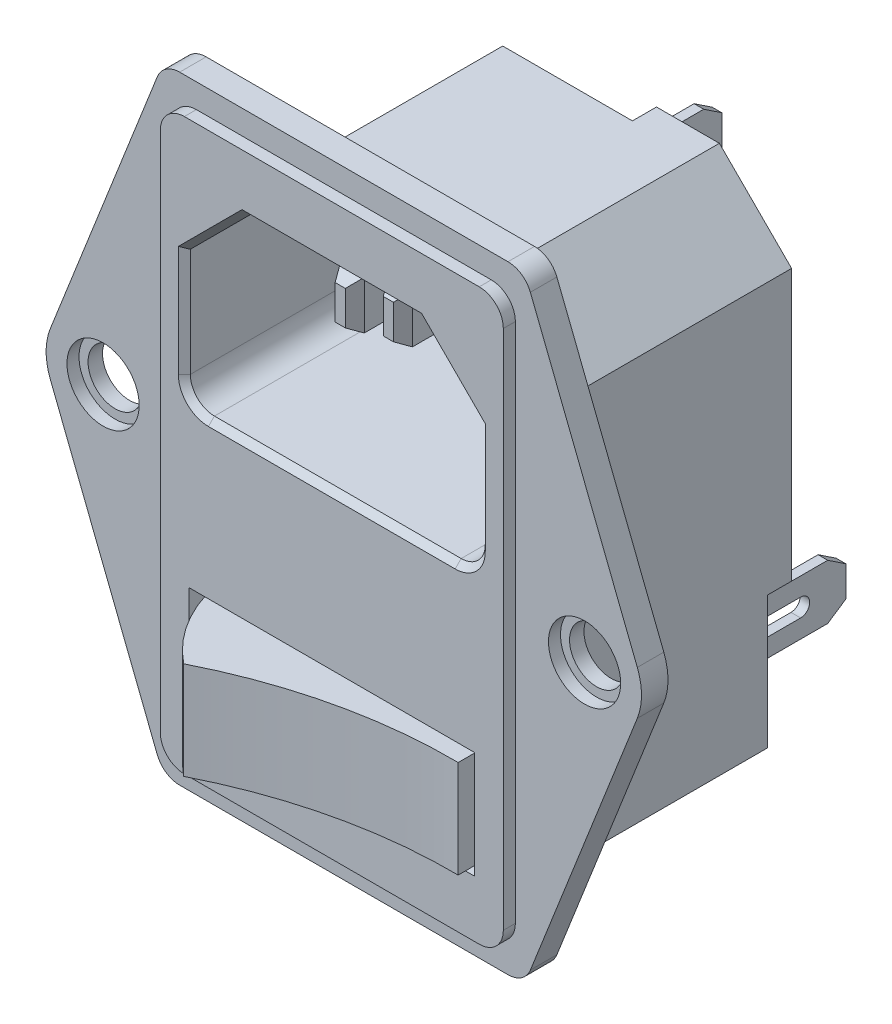
SolidWorks part; units mm, degrees
ref_plane "Спереди" through (0, 0, 0) normal (0, 0, 1) x (1, 0, 0)
ref_plane "Сверху" through (0, 0, 0) normal (0, 1, 0) x (1, 0, 0)
ref_plane "Справа" through (0, 0, 0) normal (1, 0, 0) x (0, 0, -1)
sketch "Эскиз1" plane through (0, 0, 0) normal (0, 0, 1) x (1, 0, 0)
  line L0 (-15, 25.65) -> (-25.1038, 0)
  line L1 (-15, -25.65) -> (15, -25.65)
  line L2 (-15, -25.65) -> (-15, 25.65) construction
  line L3 (-15, 25.65) -> (15, 25.65)
  line L4 (15, -25.65) -> (15, 25.65) construction
  line L5 (-15, -25.65) -> (15, 25.65) construction
  line L6 (-15, 25.65) -> (15, -25.65) construction
  line L7 (-25.1038, 0) -> (-15, -25.65)
  line L8 (0, 0) -> (0, 25.65) construction
  line L9 (25.1038, 0) -> (15, -25.65)
  line L10 (15, 25.65) -> (25.1038, 0)
  point P0 (0, 0)
  dimension "D1" = 51.3
  dimension "D2" = 30
  dimension "D3" = 137
  dimension "D4" = 68.5
extrude "Бобышка-Вытянуть1" add sketch "Эскиз1" along normal blind 2.2
sketch "Эскиз2" plane through (0, 0, 2.2) normal (0, 0, 1) x (1, 0, 0)
  line L1 (-14.25, -23.65) -> (14.25, -23.65)
  line L2 (-14.25, -23.65) -> (-14.25, 23.65)
  line L3 (-14.25, 23.65) -> (14.25, 23.65)
  line L4 (14.25, -23.65) -> (14.25, 23.65)
  line L5 (-14.25, -23.65) -> (14.25, 23.65) construction
  line L6 (-14.25, 23.65) -> (14.25, -23.65) construction
  point P0 (0, 0)
  dimension "D1" = 28.5
  dimension "D2" = 47.3
extrude "Бобышка-Вытянуть2" add sketch "Эскиз2" along normal blind 3.2 from surface at -2.2 starting at face at (0, 0, 0)
sketch "Эскиз3" plane through (0, 0, 2.2) normal (0, 0, 1) x (1, 0, 0)
  line L0 (20, 0) -> (-20, 0) construction
  circle A0 centre (-20, 0) radius 2.25
  circle A1 centre (20, 0) radius 2.25
  point P4 (0, 0)
  point P9 (-22.25, 0)
  point P10 (22.25, 0)
  dimension "D1" = 4.5
  dimension "D2" = 44.5
  dimension "D3" = 40
extrude "Вырез-Вытянуть1" cut sketch "Эскиз3" against normal blind 3.2
sketch "Эскиз4" plane through (0, 0, 2.2) normal (0, 0, 1) x (1, 0, 0)
  circle A0 centre (-20, 0) radius 3
  circle A1 centre (20, 0) radius 3
  dimension "D1" = 6
extrude "Вырез-Вытянуть2" cut sketch "Эскиз4" against normal blind 1
fillet "Скругление1" radius 2 8 edges at (15, 25.65, 1.1) (-15, 25.65, 1.1) (-15, -25.65, 1.1) (15, -25.65, 1.1) (-14.25, 23.65, 2.7) (-14.25, -23.65, 2.7) (14.25, -23.65, 2.7) (14.25, 23.65, 2.7)
fillet "Скругление2" radius 5 2 edges at (25.1038, 0, 1.1) (-25.1038, 0, 1.1)
sketch "Эскиз7" plane through (0, 0, 0) normal (0, 0, -1) x (-1, 0, 0)
  line L0 (-14, 13.75) -> (-8, 19.75)
  line L1 (-14, -19.75) -> (14, -19.75)
  line L2 (-14, -19.75) -> (-14, 13.75)
  line L3 (-8, 19.75) -> (8, 19.75)
  line L4 (14, -19.75) -> (14, 13.75)
  line L5 (-14, -19.75) -> (14, 19.75) construction
  line L6 (-14, 19.75) -> (14, -19.75) construction
  line L7 (8, 19.75) -> (14, 13.75)
  point P0 (0, 0)
  dimension "D1" = 39.5
  dimension "D2" = 28
extrude "Бобышка-Вытянуть3" add sketch "Эскиз7" along normal blind 21
sketch "Эскиз6" plane through (0, 0, 3.2) normal (0, 0, 1) x (1, 0, 0)
  line L0 (-13.6382, -25.65) -> (13.6382, -25.65) construction
  line L1 (-11.85, -18.95) -> (11.85, -18.95)
  line L2 (-11.85, -18.95) -> (-11.85, -10.05)
  line L3 (-11.85, -10.05) -> (11.85, -10.05)
  line L4 (11.85, -18.95) -> (11.85, -10.05)
  line L5 (-11.85, -18.95) -> (11.85, -10.05) construction
  line L6 (-11.85, -10.05) -> (11.85, -18.95) construction
  point P0 (0, -14.5)
  dimension "D1" = 8.9
  dimension "D2" = 23.7
  dimension "D3" = 6.7
extrude "Вырез-Вытянуть3" cut sketch "Эскиз6" against normal blind 3
sketch "Эскиз8" plane through (0, 0, -21) normal (0, 0, -1) x (-1, 0, 0)
  line L0 (8, 19.75) -> (-8, 19.75) construction
  line L1 (-14, -19.75) -> (-8.6, -19.75)
  line L2 (-14, -19.75) -> (-14, -8.75)
  line L3 (-14, -8.75) -> (-8.6, -8.75)
  line L4 (-8.6, -19.75) -> (-8.6, -8.75)
  line L5 (-2.775, 8.35) -> (2.775, 8.35)
  line L6 (-2.775, 8.35) -> (-2.775, 19.75)
  line L7 (-2.775, 19.75) -> (2.775, 19.75)
  line L8 (2.775, 8.35) -> (2.775, 19.75) construction
  line L9 (-2.775, 8.35) -> (2.775, 19.75) construction
  line L10 (-2.775, 19.75) -> (2.775, 8.35) construction
  line L11 (0, 0) -> (0, -19.75) construction
  line L12 (-14, -19.75) -> (14, -19.75) construction
  line L13 (14, -8.75) -> (8.6, -8.75)
  line L14 (8.6, -19.75) -> (8.6, -8.75)
  line L15 (14, -19.75) -> (8.6, -19.75)
  line L16 (14, -19.75) -> (14, -8.75)
  line L17 (2.775, 12.55) -> (14, 12.55)
  line L18 (14, -19.75) -> (14, 13.75) construction
  line L19 (14, 12.55) -> (14, 19.75)
  line L20 (14, 19.75) -> (2.775, 19.75)
  line L21 (2.775, 12.55) -> (2.775, 8.35)
  point P5 (0, 14.05)
  dimension "D1" = 11
  dimension "D2" = 5.4
  dimension "D3" = 7.2
  dimension "D4" = 11.4
  dimension "D5" = 5.55
extrude "Вырез-Вытянуть4" cut sketch "Эскиз8" against normal blind 2
sketch "Эскиз9" plane through (0, 0, -21) normal (0, 0, -1) x (-1, 0, 0)
  line L0 (-14, -19.75) -> (14, -19.75) construction
  line L1 (-1.5, -9.25) -> (1.5, -9.25)
  line L2 (-1.5, -9.25) -> (-1.5, -19.75)
  line L3 (-1.5, -19.75) -> (1.5, -19.75)
  line L4 (1.5, -9.25) -> (1.5, -19.75)
  line L5 (-1.5, -9.25) -> (1.5, -19.75) construction
  line L6 (-1.5, -19.75) -> (1.5, -9.25) construction
  line L7 (-14, 13.75) -> (-14, -8.75) construction
  line L8 (-6.5, 0.25) -> (-3.5, 0.25)
  line L9 (-6.5, 0.25) -> (-6.5, -7.75)
  line L10 (-6.5, -7.75) -> (-3.5, -7.75)
  line L11 (-3.5, 0.25) -> (-3.5, -7.75)
  line L12 (-6.5, 0.25) -> (-3.5, -7.75) construction
  line L13 (-6.5, -7.75) -> (-3.5, 0.25) construction
  line L14 (-9.8, 11.55) -> (-4.3, 11.55)
  line L15 (-9.8, 11.55) -> (-9.8, 6.05)
  line L16 (-9.8, 6.05) -> (-4.3, 6.05)
  line L17 (-4.3, 11.55) -> (-4.3, 6.05)
  line L18 (-9.8, 11.55) -> (-4.3, 6.05) construction
  line L19 (-9.8, 6.05) -> (-4.3, 11.55) construction
  line L20 (8, 19.75) -> (-2.775, 19.75) construction
  line L21 (0, 0) -> (0, 25.65) construction
  line L22 (-13.6382, 25.65) -> (13.6382, 25.65) construction
  line L23 (9.8, 6.05) -> (4.3, 6.05)
  line L24 (4.3, 11.55) -> (4.3, 6.05)
  line L25 (9.8, 11.55) -> (4.3, 11.55)
  line L26 (9.8, 11.55) -> (9.8, 6.05)
  line L27 (6.5, -7.75) -> (3.5, -7.75)
  line L28 (3.5, 0.25) -> (3.5, -7.75)
  line L29 (6.5, 0.25) -> (3.5, 0.25)
  line L30 (6.5, 0.25) -> (6.5, -7.75)
  point P0 (0, -14.5)
  point P7 (-5, -3.75)
  point P12 (-7.05, 8.8)
  dimension "D1" = 5.5
  dimension "D2" = 3
  dimension "D3" = 8
  dimension "D4" = 10.5
  dimension "D5" = 3
  dimension "D6" = 12
  dimension "D7" = 7.5
  dimension "D8" = 4.2
  dimension "D9" = 8.2
extrude "Бобышка-Вытянуть4" add sketch "Эскиз9" along normal blind 2.1
sketch "Эскиз10" plane through (0, 0, -19) normal (0, 0, -1) x (-1, 0, 0)
  line L0 (14, -19.75) -> (14, 13.75) construction
  line L1 (-0.4, 10.7) -> (0.4, 10.7)
  line L2 (-0.4, 10.7) -> (-0.4, 15.25)
  line L3 (-0.4, 15.25) -> (0.4, 15.25)
  line L4 (0.4, 10.7) -> (0.4, 15.25)
  line L5 (-0.4, 10.7) -> (0.4, 15.25) construction
  line L6 (-0.4, 15.25) -> (0.4, 10.7) construction
  line L7 (-10.7, -16.6) -> (-9.9, -16.6)
  line L8 (-10.7, -16.6) -> (-10.7, -12.05)
  line L9 (-10.7, -12.05) -> (-9.9, -12.05)
  line L10 (-9.9, -16.6) -> (-9.9, -12.05)
  line L11 (-10.7, -16.6) -> (-9.9, -12.05) construction
  line L12 (-10.7, -12.05) -> (-9.9, -16.6) construction
  line L13 (9.9, -16.6) -> (10.7, -16.6)
  line L14 (9.9, -16.6) -> (9.9, -12.05)
  line L15 (9.9, -12.05) -> (10.7, -12.05)
  line L16 (10.7, -16.6) -> (10.7, -12.05)
  line L17 (9.9, -16.6) -> (10.7, -12.05) construction
  line L18 (9.9, -12.05) -> (10.7, -16.6) construction
  line L19 (8.6, -19.75) -> (14, -19.75) construction
  line L20 (0, 0) -> (0, -19.75) construction
  line L21 (-14, -19.75) -> (14, -19.75) construction
  line L22 (8, 19.75) -> (-2.775, 19.75) construction
  point P0 (0, 12.975)
  point P5 (10.3, -14.325)
  point P7 (-10.3, -14.325)
  dimension "D1" = 0.8
  dimension "D2" = 4.55
  dimension "D3" = 3.3
  dimension "D4" = 3.15
  dimension "D5" = 4.5
extrude "Бобышка-Вытянуть5" add sketch "Эскиз10" along normal blind 9.8
sketch "Эскиз11" plane through (-10.7, 0, 0) normal (-1, 0, 0) x (0, 0, 1)
  line L0 (-25.05, -14.325) -> (-21.55, -14.325) construction
  line L1 (-25.05, -13.575) -> (-21.55, -13.575)
  line L2 (-25.05, -15.075) -> (-21.55, -15.075)
  line L3 (-28.8, -16.6) -> (-28.8, -12.05) construction
  arc A0 (-25.05, -13.575) -> (-25.05, -15.075) centre (-25.05, -14.325) ccw
  arc A1 (-21.55, -15.075) -> (-21.55, -13.575) centre (-21.55, -14.325) ccw
  point P2 (-23.3, -14.325)
  point P10 (-28.8, -14.325)
  point P11 (-25.8, -14.325)
  dimension "D1" = 1.5
  dimension "D2" = 3.5
  dimension "D3" = 3
extrude "Вырез-Вытянуть5" cut sketch "Эскиз11" against normal up to surface (0.8 mm away) up to face at (-9.9, -14.325, -23.9)
sketch "Эскиз12" plane through (10.7, 0, 0) normal (1, 0, 0) x (0, 0, -1)
  line L2 (25.05, -13.575) -> (21.55, -13.575)
  line L3 (21.55, -15.075) -> (25.05, -15.075)
  line L4 (25.05, -13.575) -> (21.55, -13.575)
  line L5 (21.55, -15.075) -> (25.05, -15.075)
  arc A2 (21.55, -13.575) -> (21.55, -15.075) centre (21.55, -14.325) ccw
  arc A3 (25.05, -15.075) -> (25.05, -13.575) centre (25.05, -14.325) ccw
  arc A4 (21.55, -13.575) -> (21.55, -15.075) centre (21.55, -14.325) ccw
  arc A5 (25.05, -15.075) -> (25.05, -13.575) centre (25.05, -14.325) ccw
  dimension "D1" = 0
extrude "Вырез-Вытянуть6" cut sketch "Эскиз12" against normal up to surface (0.8 mm away) up to face at (9.9, -14.325, -23.9)
sketch "Эскиз13" plane through (-0.4, 0, 0) normal (-1, 0, 0) x (0, 0, 1)
  line L0 (-21.55, 12.975) -> (-25.05, 12.975) construction
  line L1 (-21.55, 12.225) -> (-25.05, 12.225)
  line L2 (-21.55, 13.725) -> (-25.05, 13.725)
  line L3 (-28.8, 10.7) -> (-28.8, 15.25) construction
  arc A0 (-21.55, 12.225) -> (-21.55, 13.725) centre (-21.55, 12.975) ccw
  arc A1 (-25.05, 13.725) -> (-25.05, 12.225) centre (-25.05, 12.975) ccw
  point P2 (-23.3, 12.975)
  point P10 (-28.8, 12.975)
  point P12 (-25.8, 12.975)
  dimension "D1" = 1.5
  dimension "D2" = 3.5
  dimension "D3" = 3
extrude "Вырез-Вытянуть7" cut sketch "Эскиз13" against normal up to surface (0.8 mm away) up to face at (0.4, 12.975, -23.9)
chamfer "Фаска1" distance 1.5 distance2 1 6 edges at (0, 15.25, -28.8) (0, 10.7, -28.8) (-10.3, -16.6, -28.8) (-10.3, -12.05, -28.8) (10.3, -12.05, -28.8) (10.3, -16.6, -28.8)
sketch "Эскиз14" plane through (0, 0, 3.2) normal (0, 0, 1) x (1, 0, 0)
  line L0 (13.6382, 25.65) -> (-13.6382, 25.65) construction
  line L1 (-10.25, 2.85) -> (10.25, 2.85)
  line L2 (-12.25, 4.85) -> (-12.25, 13.85)
  line L3 (-7.25, 18.85) -> (7.25, 18.85)
  line L4 (12.25, 4.85) -> (12.25, 13.85)
  line L5 (-12.25, 2.85) -> (12.25, 18.85) construction
  line L6 (-12.25, 18.85) -> (12.25, 2.85) construction
  line L7 (-12.25, 13.85) -> (-7.25, 18.85)
  line L8 (7.25, 18.85) -> (12.25, 13.85)
  arc A0 (10.25, 2.85) -> (12.25, 4.85) centre (10.25, 4.85) ccw
  arc A1 (-10.25, 2.85) -> (-12.25, 4.85) centre (-10.25, 4.85) cw
  point P0 (0, 10.85)
  dimension "D4" = 2
  dimension "D1" = 24.5
  dimension "D2" = 16
  dimension "D3" = 6.8
extrude "Вырез-Вытянуть8" cut sketch "Эскиз14" against normal blind 19.7
chamfer "Фаска2" distance 0.5 angle 45 8 edges at (12.25, 9.35, 3.2) (11.6642, 3.4358, 3.2) (0, 2.85, 3.2) (-11.6642, 3.4358, 3.2) (9.75, 16.35, 3.2) (0, 18.85, 3.2) (-9.75, 16.35, 3.2) (-12.25, 9.35, 3.2)
sketch "Эскиз15" plane through (0, 0, -16.5) normal (0, 0, 1) x (1, 0, 0)
  line L0 (0, 12.85) -> (0, 0) construction
  line L1 (-1, 14.85) -> (1, 14.85)
  line L2 (-1, 14.85) -> (-1, 10.85)
  line L3 (-1, 10.85) -> (1, 10.85)
  line L4 (1, 14.85) -> (1, 10.85)
  line L5 (-1, 14.85) -> (1, 10.85) construction
  line L6 (-1, 10.85) -> (1, 14.85) construction
  line L7 (-8, 6.85) -> (-6, 6.85)
  line L8 (-8, 6.85) -> (-8, 10.85)
  line L9 (-8, 10.85) -> (-6, 10.85)
  line L10 (-6, 6.85) -> (-6, 10.85)
  line L11 (-8, 6.85) -> (-6, 10.85) construction
  line L12 (-8, 10.85) -> (-6, 6.85) construction
  line L13 (6, 6.85) -> (8, 6.85)
  line L14 (6, 6.85) -> (6, 10.85)
  line L15 (6, 10.85) -> (8, 10.85)
  line L16 (8, 6.85) -> (8, 10.85)
  line L17 (6, 6.85) -> (8, 10.85) construction
  line L18 (6, 10.85) -> (8, 6.85) construction
  line L19 (-10.25, 2.85) -> (10.25, 2.85) construction
  point P0 (0, 12.85)
  point P5 (-7, 8.85)
  point P10 (7, 8.85)
  dimension "D1" = 2
  dimension "D2" = 4
  dimension "D3" = 4
  dimension "D4" = 8
  dimension "D5" = 14
extrude "Бобышка-Вытянуть6" add sketch "Эскиз15" along normal blind 12
sketch "Эскиз16" plane through (0, 0, -4.5) normal (0, 0, 1) x (1, 0, 0)
  line L4 (1, 10.85) -> (1, 14.85)
  line L5 (1, 14.85) -> (-1, 14.85)
  line L6 (-1, 14.85) -> (-1, 10.85)
  line L7 (-1, 10.85) -> (1, 10.85)
  line L8 (1, 10.85) -> (1, 14.85)
  line L9 (1, 14.85) -> (-1, 14.85)
  line L10 (-1, 14.85) -> (-1, 10.85)
  line L11 (-1, 10.85) -> (1, 10.85)
  dimension "D1" = 0
extrude "Бобышка-Вытянуть7" add sketch "Эскиз16" along normal blind 3
chamfer "Фаска3" distance 1 angle 30 12 edges at (7, 6.85, -4.5) (6, 8.85, -4.5) (8, 8.85, -4.5) (7, 10.85, -4.5) (0, 14.85, -1.5) (-1, 12.85, -1.5) (0, 10.85, -1.5) (1, 12.85, -1.5) (-7, 10.85, -4.5) (-8, 8.85, -4.5) (-6, 8.85, -4.5) (-7, 6.85, -4.5)
sketch "Эскиз17" plane through (0, -19.75, 0) normal (0, -1, 0) x (1, 0, 0)
  line L0 (-14.8, 0) -> (-14.8, -2)
  line L1 (-24.382, 0) -> (-15.4991, 0) construction
  line L2 (-14.8, -2) -> (-14, -3)
  line L3 (-14, -19) -> (-14, 0) construction
  line L4 (-14, -3) -> (-14, 0)
  line L5 (-14, 0) -> (-14.8, 0)
  line L6 (-14, -21) -> (-8.6, -21) construction
  line L7 (-24.382, 2.2) -> (-15.4991, 2.2) construction
  line L8 (0, 0) -> (0, -23.1) construction
  line L9 (14, 0) -> (-14, 0) construction
  line L10 (1.5, -23.1) -> (-1.5, -23.1) construction
  line L11 (14, -3) -> (14, 0)
  line L12 (14.8, -2) -> (14, -3)
  line L13 (14.8, 0) -> (14.8, -2)
  line L14 (14, 0) -> (14.8, 0)
  dimension "D1" = 14.8
  dimension "D2" = 18
  dimension "D3" = 4.2
extrude "Бобышка-Вытянуть8" add sketch "Эскиз17" against normal blind 33.35
sketch "Эскиз18" plane through (0, 0, 0.2) normal (0, 0, 1) x (1, 0, 0)
  line L0 (11.85, -18.95) -> (11.85, -10.05) construction
  line L1 (-11.5, -18.55) -> (11.5, -18.55)
  line L2 (-11.5, -18.55) -> (-11.5, -10.45)
  line L3 (-11.5, -10.45) -> (11.5, -10.45)
  line L4 (11.5, -18.55) -> (11.5, -10.45)
  line L5 (-11.5, -18.55) -> (11.5, -10.45) construction
  line L6 (-11.5, -10.45) -> (11.5, -18.55) construction
  point P0 (0, -14.5)
  point P9 (11.85, -14.5)
  dimension "D1" = 23
  dimension "D2" = 8.1
extrude "Бобышка-Вытянуть9" add sketch "Эскиз18" along normal blind 5.3 and the other way up to surface from surface separate body
sketch "Эскиз19" plane through (0, -18.55, 0) normal (0, -1, 0) x (1, 0, 0)
  line L0 (11.5, 8.5) -> (-11.5, 8.5) construction
  line L1 (11.5, 8.5) -> (11.5, 0.2) construction
  line L3 (-11.5, 0.2) -> (-11.5, 10.2)
  line L4 (-11.5, 10.2) -> (11.5, 10.2)
  line L5 (11.5, 10.2) -> (11.5, 4.2)
  line L6 (-12.25, 3.2) -> (12.25, 3.2) construction
  line L8 (11.5, 0.2) -> (11.5, 8.5) construction
  arc A0 (-7, 8.5) -> (-11.5, 0.2) centre (0.4487, -0.9083) ccw
  arc A1 (-7, 8.5) -> (11.5, 4.2) centre (11.047, 44.1974) ccw
  point P0 (-7, 8.5)
  dimension "D3" = 40
  dimension "D4" = 12
  dimension "D1" = 18.5
  dimension "D2" = 1
  dimension "D5" = 10
extrude "Вырез-Вытянуть9" cut sketch "Эскиз19" against normal up to surface (8.1 mm away) up to face at (0, -10.45, 4.35)
